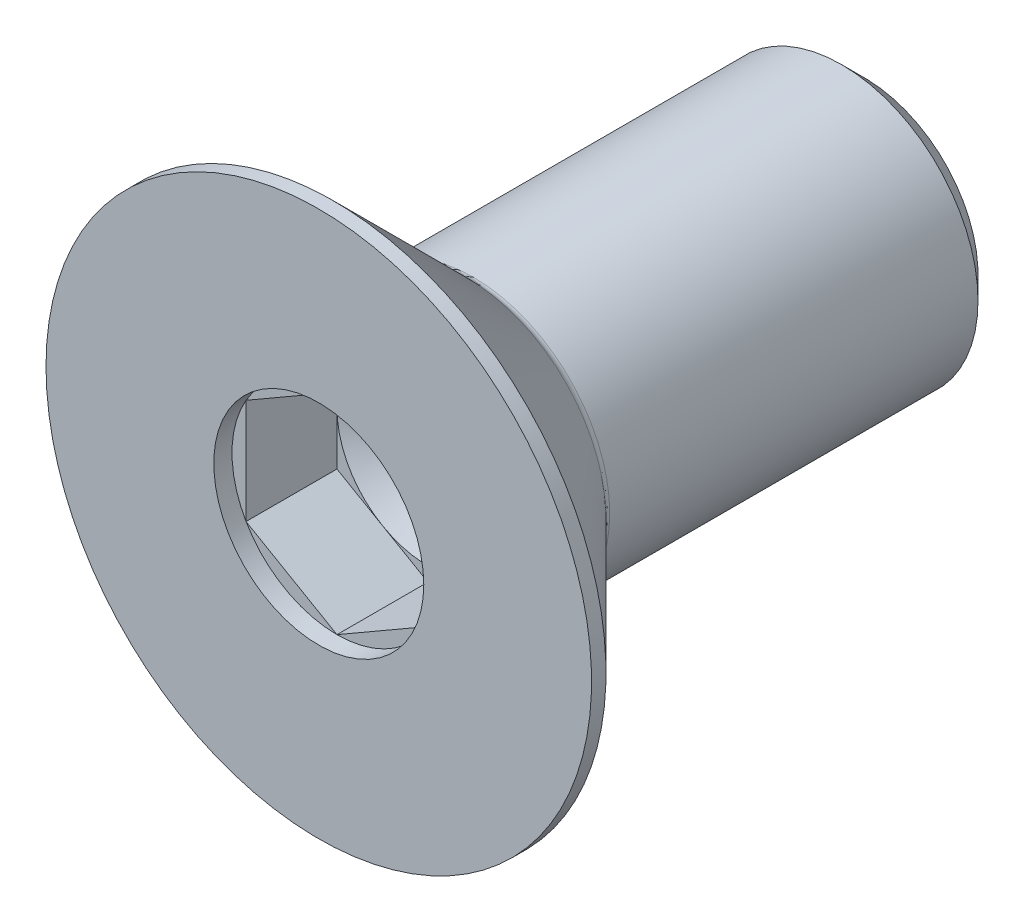
SolidWorks part; units mm, degrees
ref_plane "Front Plane" through (0, 0, 0) normal (0, 0, 1) x (1, 0, 0)
ref_plane "Top Plane" through (0, 0, 0) normal (0, 1, 0) x (1, 0, 0)
ref_plane "Right Plane" through (0, 0, 0) normal (1, 0, 0) x (0, 0, -1)
sketch "Sketch2" plane through (0, 0, 0) normal (1, 0, 0) x (0, 0, -1)
  line L0 (0, 0) -> (-19.1475, 0) construction
  line L1 (0, 0) -> (0, 3)
  line L3 (1.7, 1.5) -> (5.75, 1.5)
  line L4 (5.75, 1.5) -> (6, 1.25)
  line L5 (6, 1.25) -> (6, 0)
  line L6 (6, 0) -> (0, 0)
  line L7 (0, 3) -> (0.1586, 3)
  line L8 (0.1586, 3) -> (1.6293, 1.5293)
  arc A0 (1.6293, 1.5293) -> (1.7, 1.5) centre (1.7, 1.6) ccw
  point P11 (1.6586, 1.5)
  dimension "D4" = 0.1
  dimension "D1" = 45
  dimension "D2" = 1.7
  dimension "MVAL2" = 2.5
  dimension "D3" = 45
  dimension "MVAL" = 3
  dimension "Length" = 6
  dimension "DK" = 6
revolve "Revolve1" add sketch "Sketch2" angle 360 about L0
cosmetic thread "Cosmetic Thread1" parameters "D1"=6, "D2"=3
sketch "Sketch3" plane through (0, 0, 0) normal (0, 0, 1) x (1, 0, 0)
  line L0 (0, 0) -> (0, 1.1547) construction
  line L14 (0, 1.1547) -> (-1, 0.5774)
  line L15 (-1, 0.5774) -> (-1, -0.5774)
  line L16 (-1, -0.5774) -> (0, -1.1547)
  line L17 (0, -1.1547) -> (1, -0.5774)
  line L18 (1, -0.5774) -> (1, 0.5774)
  line L19 (1, 0.5774) -> (0, 1.1547)
  circle A0 centre (0, 0) radius 1 construction
  dimension "E1" = 2
extrude "Cut-Extrude1" cut sketch "Sketch3" against normal blind 1.2
sketch "Sketch4" plane through (0, 0, 0) normal (1, 0, 0) x (0, 0, -1)
  line L0 (0, 0) -> (6.927, 0) construction
  line L1 (1.2, 0) -> (1.2, 1)
  line L3 (1.2, 1) -> (1.7774, 0)
  line L4 (1.7774, 0) -> (1.2, 0)
  dimension "D2" = 60
  dimension "E2" = 2
  dimension "T2" = 1.2
revolve "Cut-Revolve1" cut sketch "Sketch4" angle 360 about L0
sketch "Sketch5" plane through (0, 0, 0) normal (0, 0, 1) x (1, 0, 0)
  circle A0 centre (0, 0) radius 1.1547
extrude "Cut-Extrude2" cut sketch "Sketch5" against normal blind 0.2
